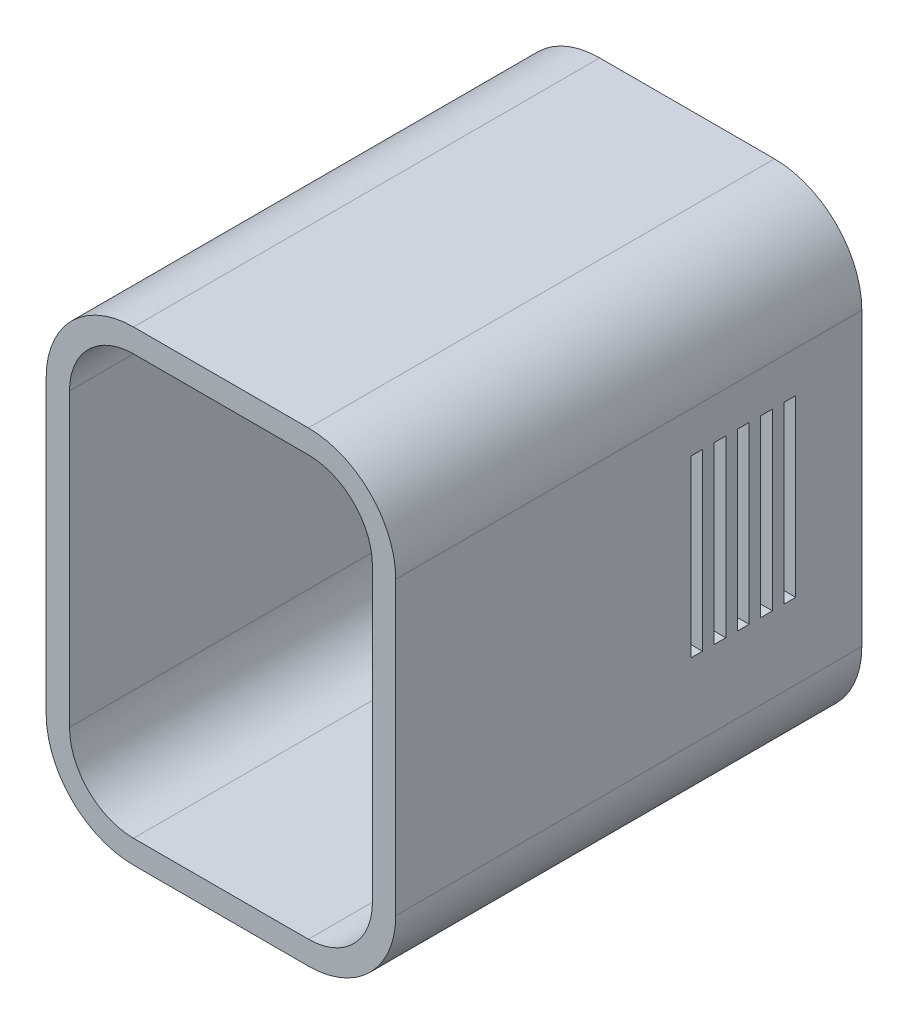
SolidWorks part; units mm, degrees
ref_plane "Front Plane" through (0, 0, 0) normal (0, 0, 1) x (1, 0, 0)
ref_plane "Top Plane" through (0, 0, 0) normal (0, 1, 0) x (1, 0, 0)
ref_plane "Right Plane" through (0, 0, 0) normal (1, 0, 0) x (0, 0, -1)
sketch "Sketch1" plane through (0, 0, 0) normal (0, 0, 1) x (1, 0, 0)
  line L1 (-7.5, -20) -> (7.5, -20)
  line L2 (-15, -12.5) -> (-15, 12.5)
  line L3 (-7.5, 20) -> (7.5, 20)
  line L4 (15, -12.5) -> (15, 12.5)
  line L5 (-15, -20) -> (15, 20) construction
  line L6 (-15, 20) -> (15, -20) construction
  arc A0 (15, -12.5) -> (7.5, -20) centre (7.5, -12.5) cw
  arc A1 (-7.5, -20) -> (-15, -12.5) centre (-7.5, -12.5) cw
  arc A2 (-15, 12.5) -> (-7.5, 20) centre (-7.5, 12.5) cw
  arc A3 (7.5, 20) -> (15, 12.5) centre (7.5, 12.5) cw
  point P1 (0, 0)
  dimension "D3" = 7.5
  dimension "D1" = 30
  dimension "D2" = 40
extrude "Boss-Extrude1" add sketch "Sketch1" along normal blind 40
shell "Shell1" thickness 2
sketch "Sketch2" plane through (0, 0, 0) normal (0, 0, -1) x (-1, 0, 0)
  line L0 (-15, -12.5) -> (-15, 12.5) construction
  line L1 (-6.35, 8) -> (-4.85, 8)
  line L2 (-6.35, 8) -> (-6.35, 1.7)
  line L3 (-6.35, 1.7) -> (-4.85, 1.7)
  line L4 (-4.85, 8) -> (-4.85, 1.7)
  line L5 (-6.35, 8) -> (-4.85, 1.7) construction
  line L6 (-6.35, 1.7) -> (-4.85, 8) construction
  line L7 (6.35, 8) -> (7.85, 8)
  line L8 (6.35, 8) -> (6.35, 1.7)
  line L9 (6.35, 1.7) -> (7.85, 1.7)
  line L10 (7.85, 8) -> (7.85, 1.7)
  line L11 (6.35, 8) -> (7.85, 1.7) construction
  line L12 (6.35, 1.7) -> (7.85, 8) construction
  line L13 (-0.2793, -8.8801) -> (1.7793, -8.8801)
  line L14 (-0.2793, -8.8801) -> (-0.2793, -5.2199)
  line L15 (-0.2793, -5.2199) -> (1.7793, -5.2199)
  line L16 (1.7793, -8.8801) -> (1.7793, -5.2199)
  line L17 (-0.2793, -8.8801) -> (1.7793, -5.2199) construction
  line L18 (-0.2793, -5.2199) -> (1.7793, -8.8801) construction
  line L19 (-7.5, 20) -> (7.5, 20) construction
  point P4 (-5.6, 4.85)
  point P9 (7.1, 4.85)
  point P10 (0.75, -7.05)
  point P15 (-5.6, 1.7)
  point P16 (7.1, 1.7)
  point P17 (-6.35, 4.85)
  point P22 (-5.6, 8)
  dimension "D1" = 12.7
  dimension "D2" = 1.5
  dimension "D3" = 1.5
  dimension "D4" = 6.3
  dimension "D5" = 6.3
  dimension "D6" = 11.9
  dimension "D7" = 6.35
  dimension "D8" = 8.65
  dimension "D9" = 12
extrude "Cut-Extrude1" cut sketch "Sketch2" against normal blind 25
sketch "Sketch3" plane through (-15, 0, 0) normal (-1, 0, 0) x (0, 0, 1)
  line L0 (7.675, -6.0085) -> (8.675, -6.0085)
  line L1 (5.675, -6.0085) -> (6.675, -6.0085)
  line L2 (5.675, -6.0085) -> (5.675, 8.9915)
  line L3 (5.675, 8.9915) -> (6.675, 8.9915)
  line L4 (6.675, -6.0085) -> (6.675, 8.9915)
  line L5 (5.675, -6.0085) -> (6.675, 8.9915) construction
  line L6 (5.675, 8.9915) -> (6.675, -6.0085) construction
  line L7 (8.675, -6.0085) -> (8.675, 8.9915)
  line L8 (7.675, 8.9915) -> (8.675, 8.9915)
  line L9 (7.675, -6.0085) -> (7.675, 8.9915)
  line L10 (9.675, -6.0085) -> (10.675, -6.0085)
  line L11 (10.675, -6.0085) -> (10.675, 8.9915)
  line L12 (9.675, 8.9915) -> (10.675, 8.9915)
  line L13 (9.675, -6.0085) -> (9.675, 8.9915)
  line L14 (11.675, -6.0085) -> (12.675, -6.0085)
  line L15 (12.675, -6.0085) -> (12.675, 8.9915)
  line L16 (11.675, 8.9915) -> (12.675, 8.9915)
  line L17 (11.675, -6.0085) -> (11.675, 8.9915)
  line L18 (13.675, -6.0085) -> (14.675, -6.0085)
  line L19 (14.675, -6.0085) -> (14.675, 8.9915)
  line L20 (13.675, 8.9915) -> (14.675, 8.9915)
  line L21 (13.675, -6.0085) -> (13.675, 8.9915)
  point P0 (6.175, 1.4915)
  dimension "D1" = 1
  dimension "D2" = 15
  dimension "D3" = 5
extrude "Cut-Extrude2" cut sketch "Sketch3" against normal through all both and the other way through all
sketch "Sketch4" plane through (0, 0, 40) normal (0, 0, 1) x (1, 0, 0)
  line L0 (13, -12.5) -> (13, 12.5) construction
  line L1 (-7.5, -18) -> (7.5, -18) construction
  line L2 (-13, 12.5) -> (-13, -12.5) construction
  line L3 (7.5, 18) -> (-7.5, 18) construction
  line L4 (15, -12.5) -> (15, 12.5)
  line L5 (7.5, 20) -> (-7.5, 20)
  line L6 (-15, 12.5) -> (-15, -12.5)
  line L7 (-7.5, -20) -> (7.5, -20)
  line L8 (15, -12.5) -> (15, 12.5)
  line L9 (7.5, 20) -> (-7.5, 20)
  line L10 (-15, 12.5) -> (-15, -12.5)
  line L11 (-7.5, -20) -> (7.5, -20)
  line L12 (13, -12.5) -> (13, 12.5)
  line L13 (-7.5, -18) -> (7.5, -18)
  line L14 (-13, 12.5) -> (-13, -12.5)
  line L15 (7.5, 18) -> (-7.5, 18)
  arc A0 (7.5, -18) -> (13, -12.5) centre (7.5, -12.5) ccw construction
  arc A1 (-13, -12.5) -> (-7.5, -18) centre (-7.5, -12.5) ccw construction
  arc A2 (-7.5, 18) -> (-13, 12.5) centre (-7.5, 12.5) ccw construction
  arc A3 (13, 12.5) -> (7.5, 18) centre (7.5, 12.5) ccw construction
  arc A4 (7.5, -20) -> (15, -12.5) centre (7.5, -12.5) ccw
  arc A5 (15, 12.5) -> (7.5, 20) centre (7.5, 12.5) ccw
  arc A6 (-7.5, 20) -> (-15, 12.5) centre (-7.5, 12.5) ccw
  arc A7 (-15, -12.5) -> (-7.5, -20) centre (-7.5, -12.5) ccw
  arc A8 (7.5, -20) -> (15, -12.5) centre (7.5, -12.5) ccw
  arc A9 (15, 12.5) -> (7.5, 20) centre (7.5, 12.5) ccw
  arc A10 (-7.5, 20) -> (-15, 12.5) centre (-7.5, 12.5) ccw
  arc A11 (-15, -12.5) -> (-7.5, -20) centre (-7.5, -12.5) ccw
  arc A12 (7.5, -18) -> (13, -12.5) centre (7.5, -12.5) ccw
  arc A13 (-13, -12.5) -> (-7.5, -18) centre (-7.5, -12.5) ccw
  arc A14 (-7.5, 18) -> (-13, 12.5) centre (-7.5, 12.5) ccw
  arc A15 (13, 12.5) -> (7.5, 18) centre (7.5, 12.5) ccw
  dimension "D1" = 0
